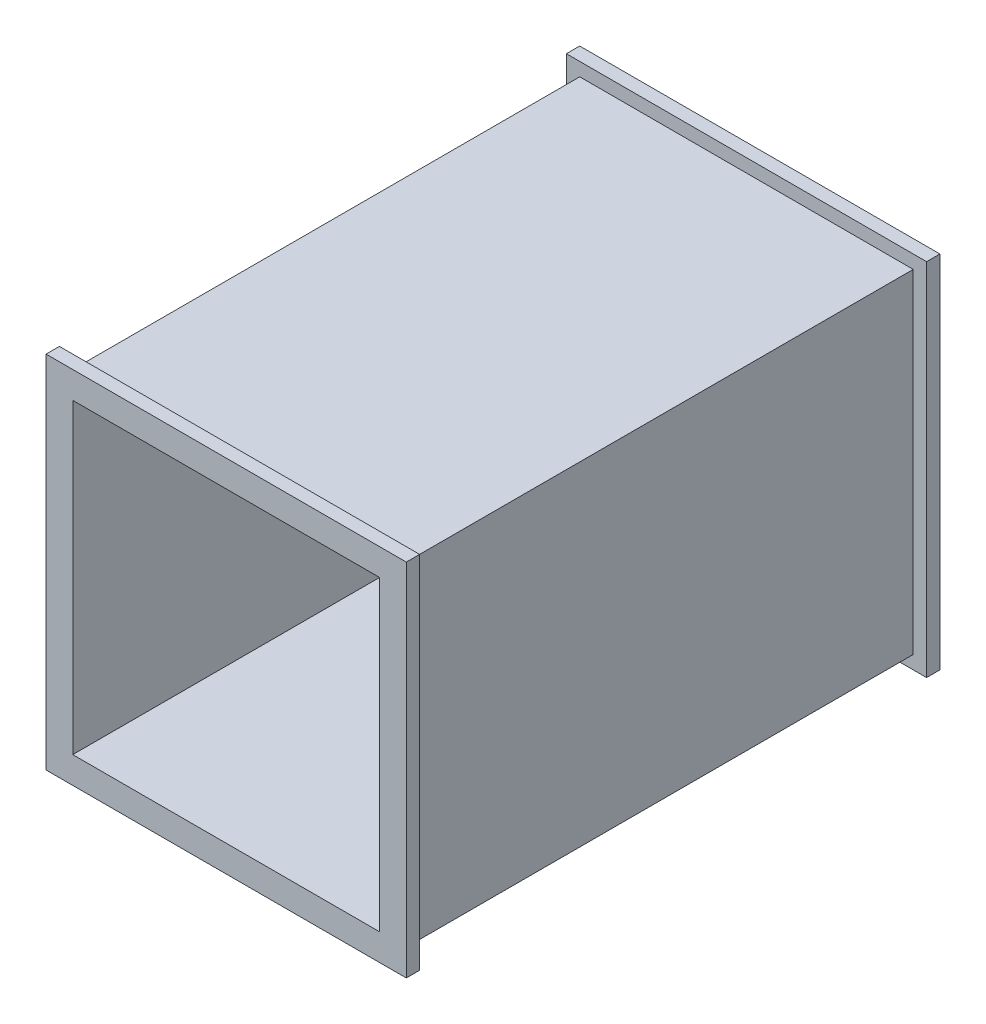
SolidWorks part; units mm, degrees
ref_plane "Front Plane" through (0, 0, 0) normal (0, 0, 1) x (1, 0, 0)
ref_plane "Top Plane" through (0, 0, 0) normal (0, 1, 0) x (1, 0, 0)
ref_plane "Right Plane" through (0, 0, 0) normal (1, 0, 0) x (0, 0, -1)
sketch "Sketch2" plane through (0, 0, 0) normal (0, 0, 1) x (1, 0, 0)
  line L1 (-62.5, 62.5) -> (62.5, 62.5)
  line L2 (-62.5, 62.5) -> (-62.5, -62.5)
  line L3 (-62.5, -62.5) -> (62.5, -62.5)
  line L4 (62.5, 62.5) -> (62.5, -62.5)
  line L5 (-62.5, 62.5) -> (62.5, -62.5) construction
  line L6 (-62.5, -62.5) -> (62.5, 62.5) construction
  point P0 (0, 0)
  dimension "D1" = 125
  dimension "D2" = 125
extrude "Boss-Extrude1" add sketch "Sketch2" along normal blind 200 contours L1 L4 L3 L2
shell "Shell1" thickness 5
sketch "Sketch3" plane through (0, 0, 0) normal (0, 0, -1) x (-1, 0, 0)
  line L0 (67.5, 67.5) -> (-67.5, 67.5)
  line L1 (-67.5, 67.5) -> (-67.5, -67.5)
  line L2 (-67.5, -67.5) -> (67.5, -67.5)
  line L3 (67.5, -67.5) -> (67.5, 67.5)
  line L4 (62.5, -62.5) -> (62.5, 62.5)
  line L5 (62.5, 62.5) -> (-62.5, 62.5)
  line L6 (-62.5, 62.5) -> (-62.5, -62.5)
  line L7 (-62.5, -62.5) -> (62.5, -62.5)
  line L8 (62.5, -62.5) -> (62.5, 62.5)
  line L9 (62.5, 62.5) -> (-62.5, 62.5)
  line L10 (-62.5, 62.5) -> (-62.5, -62.5)
  line L11 (-62.5, -62.5) -> (62.5, -62.5)
  dimension "D1" = 0
  dimension "D2" = 5
sketch "Sketch4" plane through (0, 0, 200) normal (0, 0, 1) x (1, 0, 0)
  line L0 (67.5, 67.5) -> (-67.5, 67.5)
  line L1 (-67.5, 67.5) -> (-67.5, -67.5)
  line L2 (-67.5, -67.5) -> (67.5, -67.5)
  line L3 (67.5, -67.5) -> (67.5, 67.5)
  line L4 (-62.5, 62.5) -> (-62.5, -62.5)
  line L5 (-62.5, -62.5) -> (62.5, -62.5)
  line L6 (62.5, -62.5) -> (62.5, 62.5)
  line L7 (62.5, 62.5) -> (-62.5, 62.5)
  line L8 (-62.5, 62.5) -> (-62.5, -62.5)
  line L9 (-62.5, -62.5) -> (62.5, -62.5)
  line L10 (62.5, -62.5) -> (62.5, 62.5)
  line L11 (62.5, 62.5) -> (-62.5, 62.5)
  dimension "D1" = 0
  dimension "D2" = 5
extrude "Boss-Extrude2" add sketch "Sketch4" against normal blind 5
extrude "Boss-Extrude4" add sketch "Sketch3" against normal blind 5
